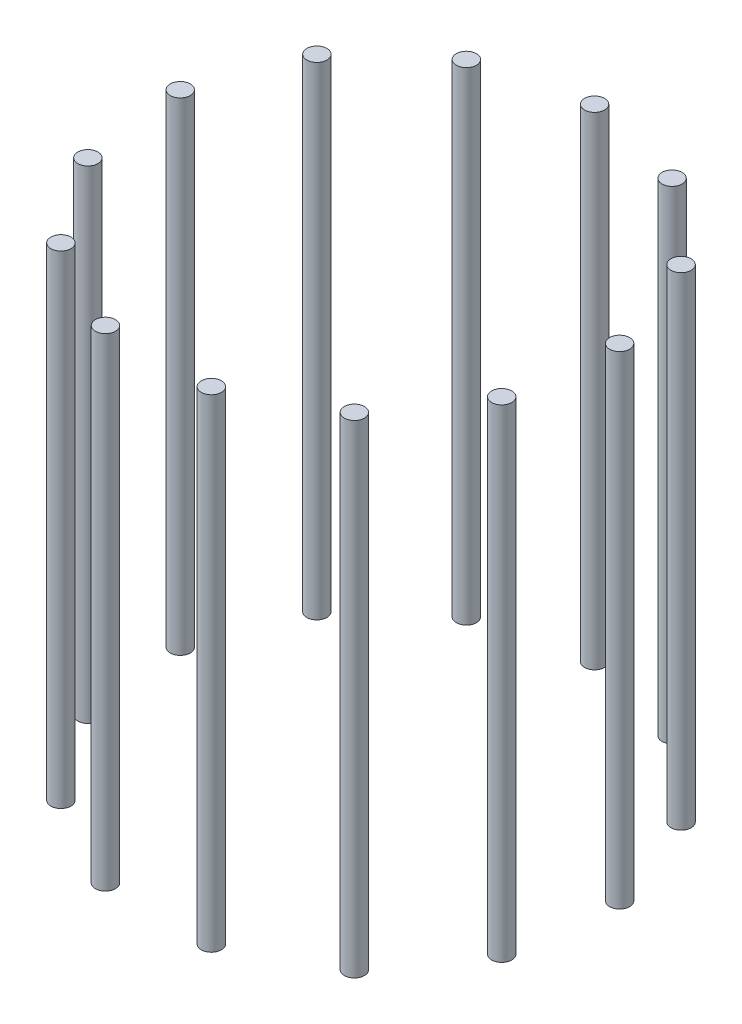
SolidWorks part; units mm, degrees
material "Chrome Stainless Steel"
ref_plane "Front Plane" through (0, 0, 0) normal (0, 0, 1) x (1, 0, 0)
ref_plane "Top Plane" through (0, 0, 0) normal (0, 1, 0) x (1, 0, 0)
ref_plane "Right Plane" through (0, 0, 0) normal (1, 0, 0) x (0, 0, -1)
sketch "Sketch1" plane through (0, 0, 0) normal (0, 1, 0) x (1, 0, 0)
  circle A0 centre (0, 5.5) radius 0.25
  circle A1 centre (2.556, 4.87) radius 0.25
  circle A2 centre (4.5264, 3.1244) radius 0.25
  circle A3 centre (5.4599, 0.663) radius 0.25
  circle A4 centre (5.1426, -1.9503) radius 0.25
  circle A5 centre (3.6472, -4.1168) radius 0.25
  circle A6 centre (1.3162, -5.3402) radius 0.25
  circle A7 centre (-1.3162, -5.3402) radius 0.25
  circle A8 centre (-3.6472, -4.1168) radius 0.25
  circle A9 centre (-5.1426, -1.9503) radius 0.25
  circle A10 centre (-5.4599, 0.663) radius 0.25
  circle A11 centre (-4.5264, 3.1244) radius 0.25
  circle A12 centre (-2.556, 4.87) radius 0.25
  point P30 (0, 0)
  dimension "D3" = 0.5
  dimension "D2" = 5.5
  dimension "D4" = 13
extrude "pinovi" add sketch "Sketch1" against normal blind 12
